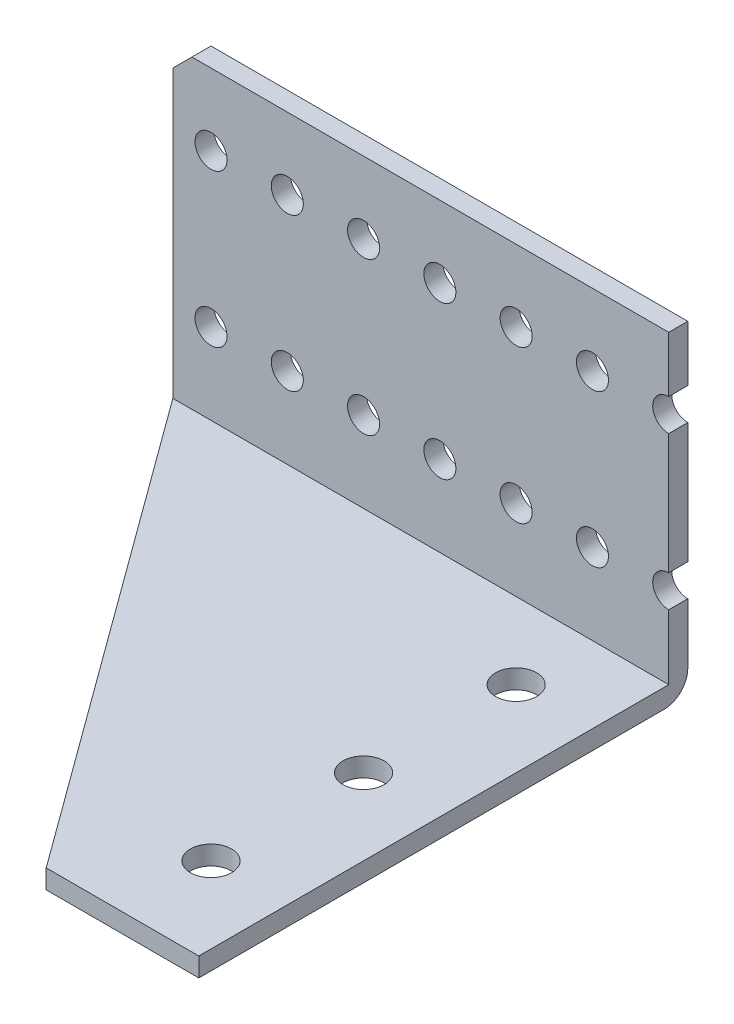
SolidWorks part; units mm, degrees
ref_plane "Front Plane" through (0, 0, 0) normal (0, 0, 1) x (1, 0, 0)
ref_plane "Top Plane" through (0, 0, 0) normal (0, 1, 0) x (1, 0, 0)
ref_plane "Right Plane" through (0, 0, 0) normal (1, 0, 0) x (0, 0, -1)
sketch "Sketch1" plane through (0, 0, 0) normal (0, 1, 0) x (1, 0, 0)
  line L0 (41.275, -40.7035) -> (41.275, 40.7035)
  line L1 (41.275, 40.7035) -> (-41.275, 40.7035)
  line L3 (-41.275, -40.7035) -> (-41.275, 40.7035)
  line L4 (-41.275, -40.7035) -> (41.275, -40.7035)
  line L5 (41.275, 40.7035) -> (-41.275, -40.7035) construction
  line L6 (0, -55) -> (0, 55) construction
  line L7 (-55, 0) -> (55, 0) construction
  point P2 (0, 0)
  dimension "D2" = 81.407
  dimension "D1" = 82.55
extrude "Boss-Extrude1" add sketch "Sketch1" along normal blind 3.175 from offset 34.925 offset against normal yes
sketch "Sketch3" plane through (0, -31.75, 0) normal (0, 1, 0) x (1, 0, 0)
  line L0 (41.275, 37.5285) -> (-41.275, 37.5285)
  line L1 (-41.275, 37.5285) -> (-41.275, 40.7035)
  line L2 (-41.275, 40.7035) -> (41.275, 40.7035)
  line L4 (41.275, 37.5285) -> (41.275, 40.7035)
  line L5 (-41.275, 40.7035) -> (-41.275, -40.7035) construction
  line L6 (41.275, -40.7035) -> (41.275, 40.7035) construction
  line L7 (41.275, 40.7035) -> (-41.275, 40.7035) construction
  dimension "D1" = 3.175
extrude "Boss-Extrude2" add sketch "Sketch3" along normal blind 50.8
hole_wizard "#10 Clearance Hole2" positions "Sketch7" profile "Sketch6" hole size "#10" standard "ANSI Inch" end condition through all
sketch "Sketch7" plane through (0, 0, -40.7035) normal (0, 0, -1) x (-1, 0, 0)
  line L2 (-41.275, -18.288) -> (34.925, -18.288) construction
  line L5 (-41.275, 7.112) -> (34.925, 7.112) construction
  line L8 (41.275, 19.05) -> (41.275, -34.925) construction
  line L9 (-41.275, 19.05) -> (-41.275, -34.925) construction
  line L10 (-41.275, 19.05) -> (41.275, 19.05) construction
  point P56 (22.225, 7.112)
  point P57 (9.525, 7.112)
  point P58 (-3.175, 7.112)
  point P59 (-15.875, 7.112)
  point P61 (-28.575, 7.112)
  point P118 (22.225, -18.288)
  point P119 (9.525, -18.288)
  point P120 (-3.175, -18.288)
  point P121 (-15.875, -18.288)
  point P123 (-28.575, -18.288)
  point P157 (34.925, 7.112)
  point P159 (34.925, -18.288)
  point P185 (-41.275, 7.112)
  point P189 (-41.275, -18.288)
  dimension "D1" = 6.35
  dimension "D2" = 11.938
  dimension "D3" = 12.7
  dimension "D4" = 25.4
  dimension "D5" = 12.7
  dimension "D6" = 12.7
  dimension "D7" = 12.7
  dimension "D8" = 12.7
  dimension "D10" = 12.7
sketch "Sketch6" plane through (-22.225, 7.112, -40.7035) normal (1, 0, 0) x (0, 1, 0)
  line L0 (0, 0) -> (0, 81.407)
  line L1 (0, 81.407) -> (2.667, 81.407)
  line L2 (2.667, 81.407) -> (2.667, 0)
  line L5 (2.667, 0) -> (0, 0)
  line L11 (0, -6.35) -> (0, 107.95) construction
  dimension "Thru Hole Dia." = 5.334
  dimension "Thru Hole Depth" = 81.407
chamfer "Chamfer1" distance 3.175 angle 45 1 edges at (-41.275, 19.05, -39.116)
fillet "Fillet2" radius 3.937 1 edges at (0, -34.925, -40.7035)
sketch "Sketch9" plane through (0, -34.925, 0) normal (0, -1, 0) x (1, 0, 0)
  line L2 (41.275, -40.7035) -> (-41.275, -40.7035) construction
  line L3 (41.275, 40.7035) -> (41.275, -36.7665) construction
  line L5 (-41.275, -37.5285) -> (-41.275, 40.7035)
  line L6 (-41.275, 40.7035) -> (41.275, 40.7035) construction
  line L7 (28.575, -40.7035) -> (28.575, 40.7035) construction
  line L10 (-41.275, -37.5285) -> (15.875, 40.7035)
  line L11 (15.875, 40.7035) -> (-41.275, 40.7035)
  line L12 (41.275, 40.7035) -> (41.275, -36.7665) construction
  line L14 (-41.275, -36.7665) -> (-41.275, 40.7035) construction
  line L16 (-41.275, -37.5285) -> (41.275, -37.5285) construction
  circle A0 centre (34.925, 1.4605) radius 3.429 construction
  circle A1 centre (34.925, -11.2395) radius 3.429 construction
  circle A2 centre (34.925, -23.9395) radius 3.429 construction
  circle A3 centre (28.575, -24.8285) radius 3.429
  circle A7 centre (28.575, 0.5715) radius 3.429
  circle A8 centre (28.575, 25.9715) radius 3.429
  dimension "D3" = 6.858
  dimension "D7" = 16.764
  dimension "D9" = 6.858
  dimension "D10" = 0
  dimension "D11" = 3
  dimension "D12" = 25.4
  dimension "D2" = 12.7
  dimension "D4" = 12.7
  dimension "D5" = 12.7
  dimension "D6" = 6.35
  dimension "D8" = 25.4
  dimension "D13" = 12.7
extrude "Cut-Extrude2" cut sketch "Sketch9" against normal through all
